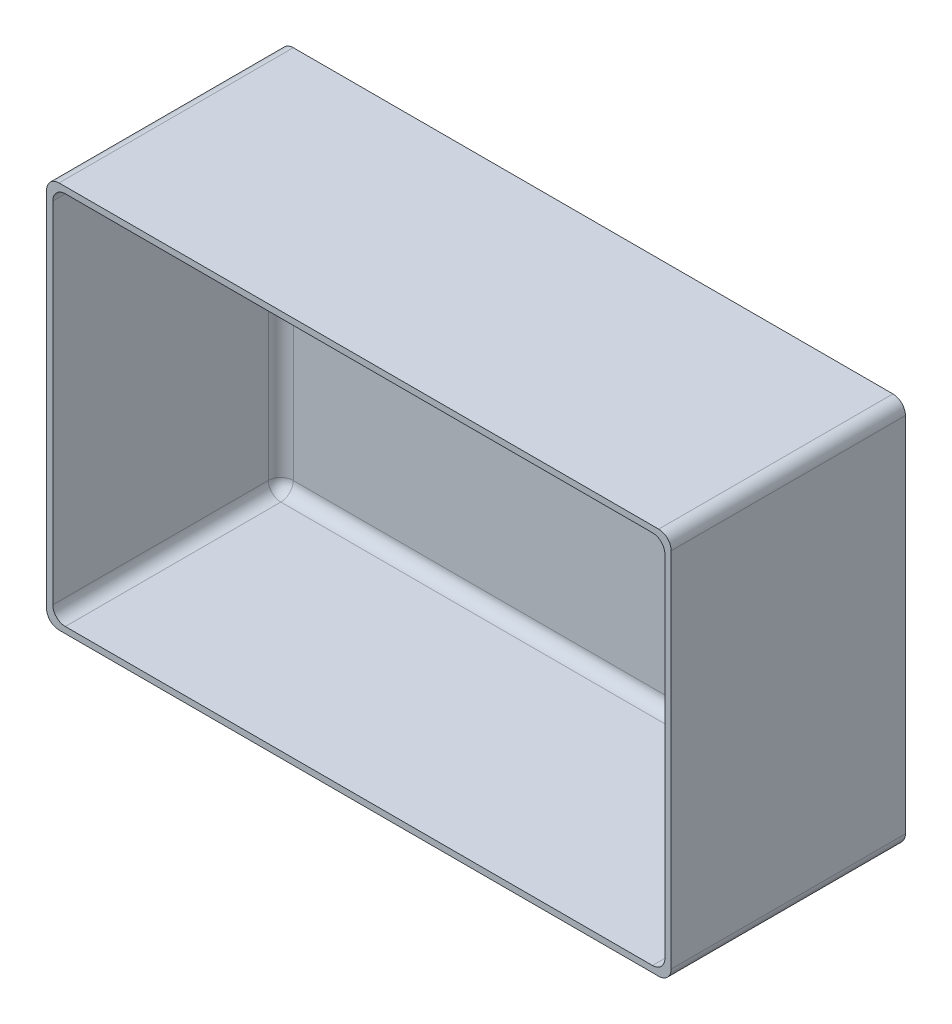
SolidWorks part; units mm, degrees
ref_plane "Plan de face" through (0, 0, 0) normal (0, 0, 1) x (1, 0, 0)
ref_plane "Plan de dessus" through (0, 0, 0) normal (0, 1, 0) x (1, 0, 0)
ref_plane "Plan de droite" through (0, 0, 0) normal (1, 0, 0) x (0, 0, -1)
sketch "Esquisse1" plane through (0, 0, 0) normal (0, 0, 1) x (1, 0, 0)
  line L1 (-40, 24.8) -> (40, 24.8)
  line L2 (-40, 24.8) -> (-40, -24.8)
  line L3 (-40, -24.8) -> (40, -24.8)
  line L4 (40, 24.8) -> (40, -24.8)
  line L5 (-40, 24.8) -> (40, -24.8) construction
  line L6 (-40, -24.8) -> (40, 24.8) construction
  point P0 (0, 0)
  dimension "D1" = 80
  dimension "D2" = 49.6
extrude "Boss.-Extru.1" add sketch "Esquisse1" along normal blind 30
shell "Coque1" thickness 0.8
fillet "Congé1" radius 1.6 12 edges at (39.2, 0, 0.8) (-39.2, 0, 0.8) (0, -24, 0.8) (39.2, -24, 15.4) (-39.2, -24, 15.4) (39.2, 24, 15.4) (0, 24, 0.8) (-39.2, 24, 15.4) (40, -24.8, 15) (-40, 24.8, 15) (40, 24.8, 15) (-40, -24.8, 15)
equation "\"longueur_ext\"= 80"
equation "\"D1@Esquisse1\"=\"longueur_ext\""
equation "\"largeur_ext\"= 49.6"
equation "\"D2@Esquisse1\"=\"largeur_ext\""
equation "\"profondeur_ext\"=30"
equation "\"D1@Boss.-Extru.1\"=\"profondeur_ext\""
equation "\"parois\"=0.8"
equation "\"D1@Coque1\"=\"parois\""
